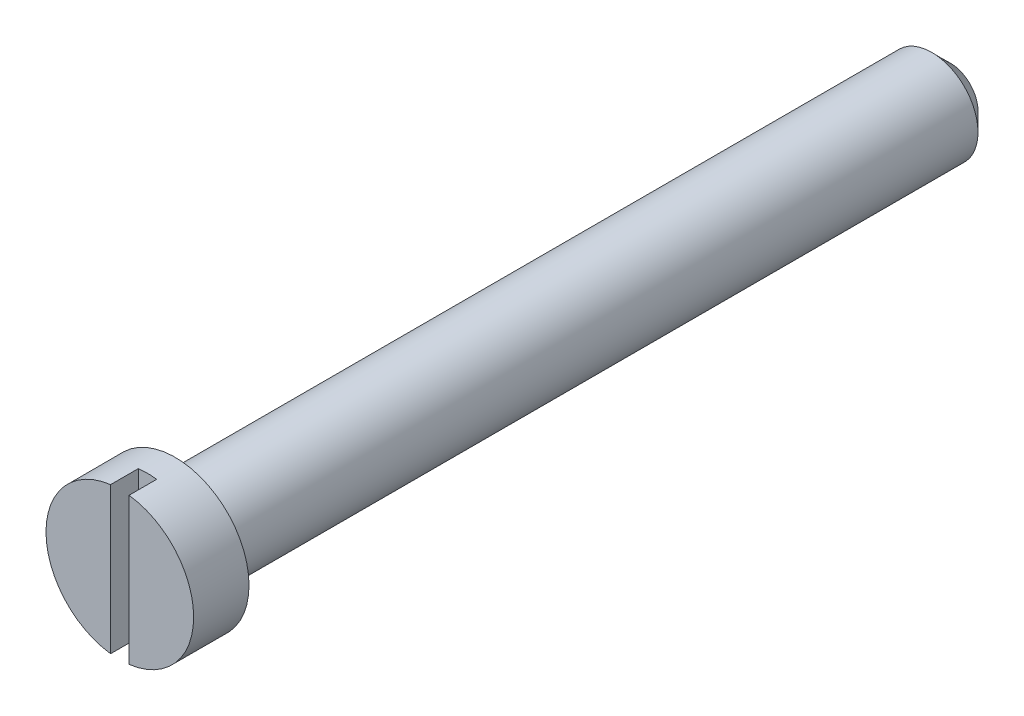
SolidWorks part; units mm, degrees
material "Простая углеродистая сталь"
ref_plane "Спереди" through (0, 0, 0) normal (0, 0, 1) x (1, 0, 0)
ref_plane "Сверху" through (0, 0, 0) normal (0, 1, 0) x (1, 0, 0)
ref_plane "Справа" through (0, 0, 0) normal (1, 0, 0) x (0, 0, -1)
sketch "Эскиз1" plane through (0, 0, 0) normal (0, 0, 1) x (1, 0, 0)
  circle A0 centre (0, 0) radius 2.5
  dimension "D1" = 5
extrude "Бобышка-Вытянуть1" add sketch "Эскиз1" along normal blind 45
cosmetic thread "Условное изображение резьбы1" parameters "D1"=10, "D2"=4
sketch "Эскиз2" plane through (0, 0, 45) normal (0, 0, 1) x (1, 0, 0)
  circle A0 centre (0, 0) radius 4
  dimension "D1" = 8
extrude "Бобышка-Вытянуть2" add sketch "Эскиз2" against normal blind 3
chamfer "Фаска1" distance 1 angle 45 1 edges at (2.5, 0, 0)
sketch "Эскиз3" plane through (0, 0, 45) normal (0, 0, 1) x (1, 0, 0)
  line L0 (0, 0) -> (0, 4) construction
  line L1 (-0.5, -4) -> (-0.5, 4)
  line L2 (-0.5, -4) -> (0.5, -4)
  line L3 (-0.5, 4) -> (0.5, 4)
  line L4 (0.5, -4) -> (0.5, 4)
  line L5 (0, 4) -> (0, -4) construction
  circle A0 centre (0, 0) radius 4 construction
  dimension "D1" = 1
extrude "Вырез-Вытянуть1" cut sketch "Эскиз3" against normal blind 1.5
